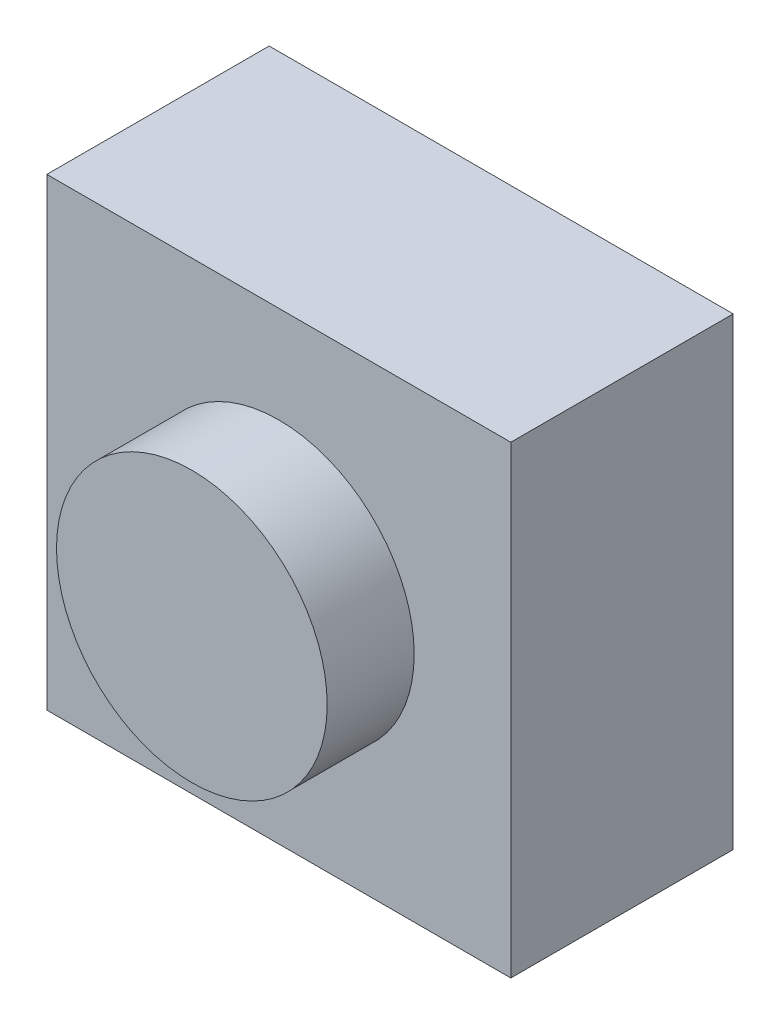
SolidWorks part; units mm, degrees
ref_plane "Front Plane" through (0, 0, 0) normal (0, 0, 1) x (1, 0, 0)
ref_plane "Top Plane" through (0, 0, 0) normal (0, 1, 0) x (1, 0, 0)
ref_plane "Right Plane" through (0, 0, 0) normal (1, 0, 0) x (0, 0, -1)
sketch "Sketch1" plane through (0, 0, 0) normal (0, 0, 1) x (1, 0, 0)
  line L1 (-149.9988, 82.9771) -> (-143.9028, 82.9771)
  line L2 (-149.9988, 82.9771) -> (-149.9988, 76.8811)
  line L3 (-149.9988, 76.8811) -> (-143.9028, 76.8811)
  line L4 (-143.9028, 82.9771) -> (-143.9028, 76.8811)
  line L5 (-149.9988, 82.9771) -> (-143.9028, 76.8811) construction
  line L6 (-149.9988, 76.8811) -> (-143.9028, 82.9771) construction
  point P0 (-146.9508, 79.9291)
  dimension "D1" = 6.096
extrude "Boss-Extrude1" add sketch "Sketch1" along normal blind 2.921
sketch "Sketch2" plane through (0, 0, 2.921) normal (0, 0, 1) x (1, 0, 0)
  line L0 (-146.9508, 82.9771) -> (-146.9508, 79.9291)
  line L1 (-143.9028, 82.9771) -> (-149.9988, 82.9771) construction
  line L2 (-146.9508, 79.9291) -> (-143.9028, 79.9291)
  line L3 (-143.9028, 76.8811) -> (-143.9028, 82.9771) construction
  line L4 (-146.9508, 79.9291) -> (-146.9508, 76.8811)
  line L5 (-149.9988, 76.8811) -> (-143.9028, 76.8811) construction
  line L6 (-146.9508, 79.9291) -> (-149.9988, 79.9291)
  line L7 (-149.9988, 82.9771) -> (-149.9988, 76.8811) construction
  circle A0 centre (-146.9508, 79.9291) radius 1.778
extrude "Boss-Extrude2" add sketch "Sketch2" along normal blind 1.143 contours A0
